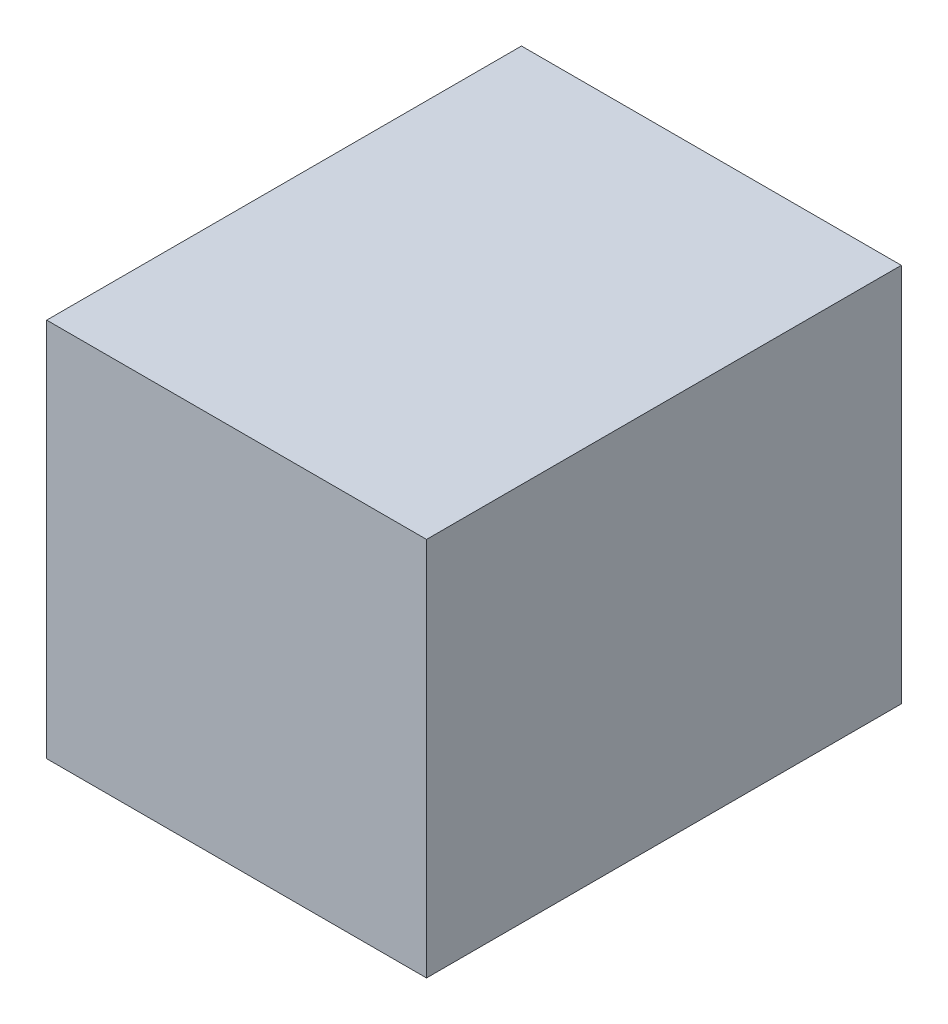
SolidWorks part; units mm, degrees
ref_plane "Front Plane" through (0, 0, 0) normal (0, 0, 1) x (1, 0, 0)
ref_plane "Top Plane" through (0, 0, 0) normal (0, 1, 0) x (1, 0, 0)
ref_plane "Right Plane" through (0, 0, 0) normal (1, 0, 0) x (0, 0, -1)
sketch "ProfileS" plane through (0, 0, 0) normal (0, 1, 0) x (1, 0, 0)
  line L1 (-0.4, 0.5) -> (0.4, 0.5)
  line L2 (-0.4, 0.5) -> (-0.4, -0.5)
  line L3 (-0.4, -0.5) -> (0.4, -0.5)
  line L4 (0.4, 0.5) -> (0.4, -0.5)
  line L5 (-0.4, 0.5) -> (0.4, -0.5) construction
  line L6 (-0.4, -0.5) -> (0.4, 0.5) construction
  point P0 (0, 0)
  dimension "Width" = 0.8
  dimension "Length" = 1
extrude "Profile" add sketch "ProfileS" along normal blind 0.8
